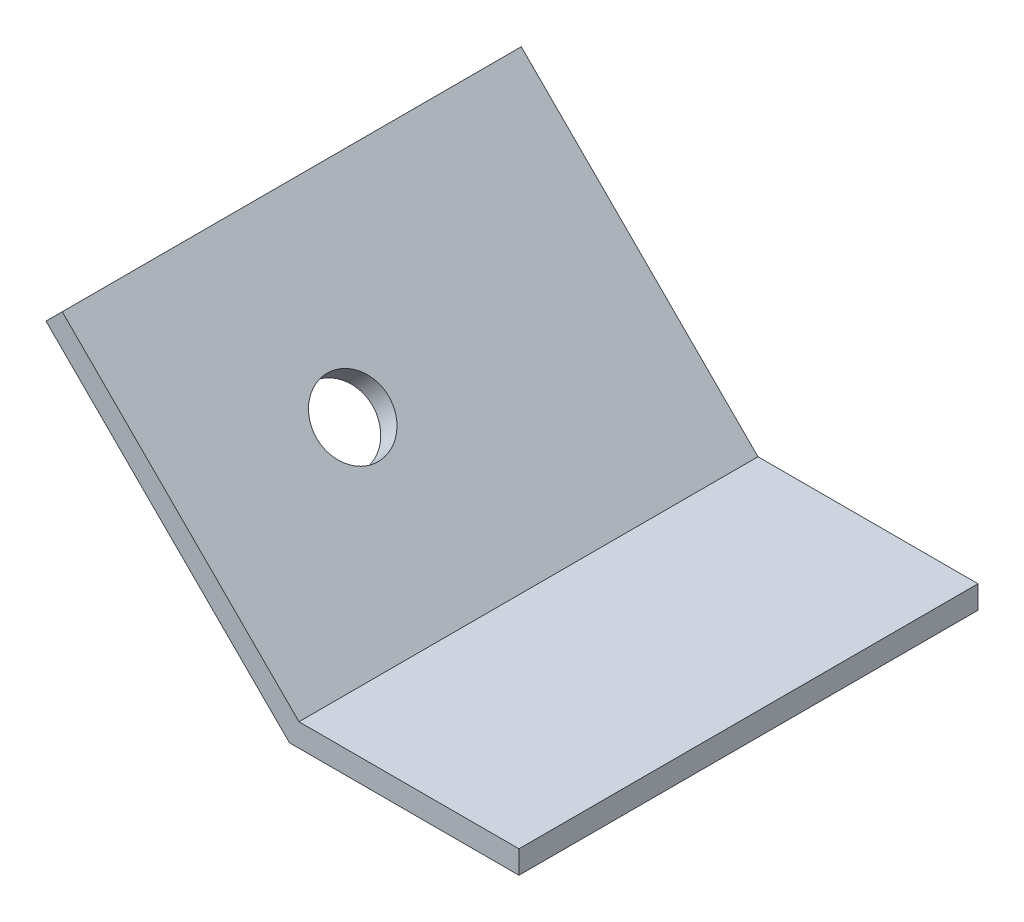
SolidWorks part; units mm, degrees
material "6061 Alloy"
ref_plane "Front Plane" through (0, 0, 0) normal (0, 0, 1) x (1, 0, 0)
ref_plane "Top Plane" through (0, 0, 0) normal (0, 1, 0) x (1, 0, 0)
ref_plane "Right Plane" through (0, 0, 0) normal (1, 0, 0) x (0, 0, -1)
sketch "Sketch1" plane through (0, 0, 0) normal (0, 0, 1) x (1, 0, 0)
  line L0 (-26.9408, 26.9408) -> (0, 0)
  line L1 (0, 0) -> (25.4, 0)
  dimension "D1" = 135
  dimension "D2" = 25.4
  dimension "D3" = 38.1
extrude "base" add sketch "Sketch1" along normal blind 50.8 thin thin type one direction reverse wall 2.54
sketch "Sketch2" plane through (1.7961, 1.7961, 0) normal (0.7071, 0.7071, 0) x (0, 0, -1)
  line L4 (0, 1.0521) -> (0, 38.1)
  line L5 (0, 38.1) -> (-50.8, 38.1)
  line L6 (-50.8, 38.1) -> (-50.8, 1.0521)
  line L7 (-50.8, 1.0521) -> (0, 1.0521)
  line L8 (0, 1.0521) -> (0, 38.1)
  line L9 (0, 38.1) -> (-50.8, 38.1)
  line L10 (-50.8, 38.1) -> (-50.8, 1.0521)
  line L11 (-50.8, 1.0521) -> (0, 1.0521)
  circle A0 centre (-31.75, 19.5761) radius 4
  point P4 (-25.4, 38.1)
  point P7 (-50.8, 19.5761)
  dimension "D1" = 8
  dimension "D3" = 19.05
  dimension "D2" = 0
extrude "axle hole" cut sketch "Sketch2" against normal up to next contours A0
